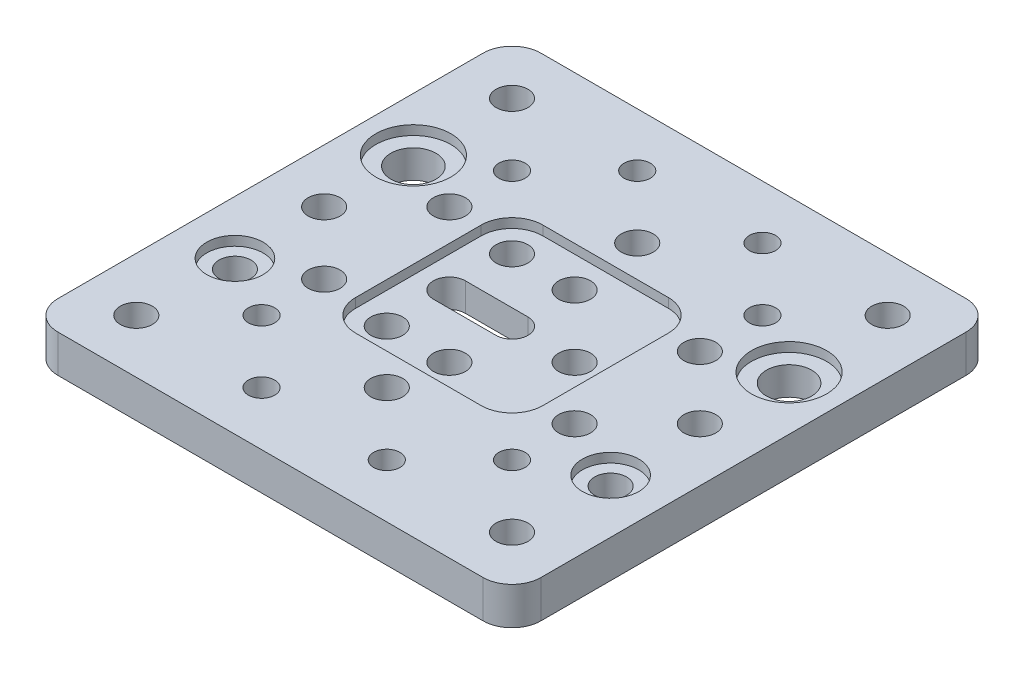
SolidWorks part; units mm, degrees
material "6061-T6 (SS)"
ref_plane "Front Plane" through (0, 0, 0) normal (0, 0, 1) x (1, 0, 0)
ref_plane "Top Plane" through (0, 0, 0) normal (0, 1, 0) x (1, 0, 0)
ref_plane "Right Plane" through (0, 0, 0) normal (1, 0, 0) x (0, 0, -1)
sketch "Sketch1" plane through (0, 0, 0) normal (0, 1, 0) x (1, 0, 0)
  line L0 (-23.7657, 0) -> (0, 0) construction
  line L1 (33.94, -38.575) -> (-33.94, -38.575)
  line L2 (38.575, -33.94) -> (38.575, 33.94)
  line L3 (33.94, 38.575) -> (-33.94, 38.575)
  line L4 (-38.575, -33.94) -> (-38.575, 33.94)
  line L5 (38.575, -38.575) -> (-38.575, 38.575) construction
  line L6 (38.575, 38.575) -> (-38.575, -38.575) construction
  line L7 (0, 0) -> (0, 28.9978) construction
  line L8 (0, 0) -> (-10, 0) construction
  line L9 (0, -2.55) -> (-10, -2.55)
  line L10 (0, 2.55) -> (-10, 2.55)
  arc A0 (-33.94, 38.575) -> (-38.575, 33.94) centre (-33.94, 33.94) ccw
  arc A1 (38.575, 33.94) -> (33.94, 38.575) centre (33.94, 33.94) ccw
  arc A2 (-33.94, -38.575) -> (-38.575, -33.94) centre (-33.94, -33.94) cw
  arc A3 (33.94, -38.575) -> (38.575, -33.94) centre (33.94, -33.94) ccw
  circle A4 centre (-30, 14.25) radius 3.6
  circle A5 centre (-20, 10) radius 2.55
  circle A7 centre (0, 20) radius 2.55
  circle A8 centre (0, 10) radius 2.55
  circle A9 centre (-10, 10) radius 2.55
  circle A11 centre (-30, 30) radius 2.55
  circle A12 centre (-30, 0) radius 2.55
  circle A13 centre (30, 30) radius 2.55
  circle A16 centre (30, 14.25) radius 3.6
  circle A17 centre (30, 0) radius 2.55
  circle A18 centre (20, 10) radius 2.55
  circle A19 centre (20, -10) radius 2.55
  circle A21 centre (-30, -30) radius 2.55
  circle A22 centre (30, -30) radius 2.55
  circle A25 centre (-20, -10) radius 2.55
  circle A27 centre (0, -20) radius 2.55
  circle A28 centre (0, -10) radius 2.55
  circle A29 centre (-10, -10) radius 2.55
  circle A30 centre (10, 0) radius 2.55
  arc A31 (0, -2.55) -> (0, 2.55) centre (0, 0) ccw
  arc A32 (-10, 2.55) -> (-10, -2.55) centre (-10, 0) ccw
  circle A33 centre (30, -14.25) radius 2.55
  circle A34 centre (-30, -14.25) radius 2.55
  point P0 (0, 0)
  point P75 (-5, 0)
  dimension "D2" = 4.635
  dimension "D3" = 5.1
  dimension "D4" = 7.2
  dimension "D12" = 10
  dimension "D1" = 77.15
  dimension "D5" = 40
  dimension "D6" = 60
  dimension "D7" = 40
  dimension "D9" = 20
  dimension "D10" = 28.5
  dimension "D11" = 60
  dimension "D13" = 10
  dimension "D14" = 10
  dimension "D15" = 5.1
extrude "Boss-Extrude1" add sketch "Sketch1" along normal blind 6
hole_wizard "M5x0.8 Tapped Hole1" positions "Sketch4" profile "Sketch3" tap size "M5x0.8" standard "ANSI Metric" end condition through all
sketch "Sketch4" plane through (0, 6, 0) normal (0, 1, 0) x (1, 0, 0)
  line L0 (-17.7377, 0) -> (0, 0) construction
  line L1 (0, 0) -> (0, 30.1375) construction
  point P0 (-20, 20)
  point P2 (-10, 30)
  point P11 (10, 30)
  point P12 (20, 20)
  point P13 (20, -20)
  point P14 (10, -30)
  point P15 (-10, -30)
  point P16 (-20, -20)
  dimension "D1" = 20
  dimension "D2" = 40
  dimension "D3" = 40
  dimension "D4" = 60
sketch "Sketch3" plane through (-20, 6, -20) normal (1, 0, 0) x (0, 0, 1)
  line L0 (0, 0) -> (0, 6)
  line L1 (0, 6) -> (2.1, 6)
  line L2 (2.1, 6) -> (2.1, 0)
  line L5 (2.1, 0) -> (0, 0)
  line L11 (0, -6.35) -> (0, 107.95) construction
  dimension "Thru Tap Drill Dia." = 4.2
  dimension "Thru Tap Drill Depth" = 6
cosmetic thread "Hole Thread1" parameters "D2"=5
cosmetic thread "Hole Thread2" parameters "D2"=5
cosmetic thread "Hole Thread3" parameters "D2"=5
cosmetic thread "Hole Thread4" parameters "D2"=5
cosmetic thread "Hole Thread5" parameters "D2"=5
cosmetic thread "Hole Thread6" parameters "D2"=5
cosmetic thread "Hole Thread7" parameters "D2"=5
cosmetic thread "Hole Thread8" parameters "D2"=5
sketch "Sketch2" plane through (0, 6, 0) normal (0, 1, 0) x (1, 0, 0)
  line L1 (10.03, -14.95) -> (-10.03, -14.95)
  line L2 (14.95, -10.03) -> (14.95, 10.03)
  line L3 (10.03, 14.95) -> (-10.03, 14.95)
  line L4 (-14.95, -10.03) -> (-14.95, 10.03)
  line L5 (14.95, -14.95) -> (-14.95, 14.95) construction
  line L6 (14.95, 14.95) -> (-14.95, -14.95) construction
  circle A0 centre (-30, 14.25) radius 6
  circle A1 centre (30, 14.25) radius 6
  circle A2 centre (30, -14.25) radius 4.5
  circle A3 centre (-30, -14.25) radius 4.5
  arc A4 (-10.03, 14.95) -> (-14.95, 10.03) centre (-10.03, 10.03) ccw
  arc A5 (10.03, -14.95) -> (14.95, -10.03) centre (10.03, -10.03) ccw
  arc A6 (14.95, 10.03) -> (10.03, 14.95) centre (10.03, 10.03) ccw
  arc A7 (-10.03, -14.95) -> (-14.95, -10.03) centre (-10.03, -10.03) cw
  point P12 (0, 0)
  dimension "D1" = 12
  dimension "D2" = 9
  dimension "D4" = 4.92
  dimension "D3" = 29.9
extrude "Cut-Extrude1" cut sketch "Sketch2" against normal blind 1.5
